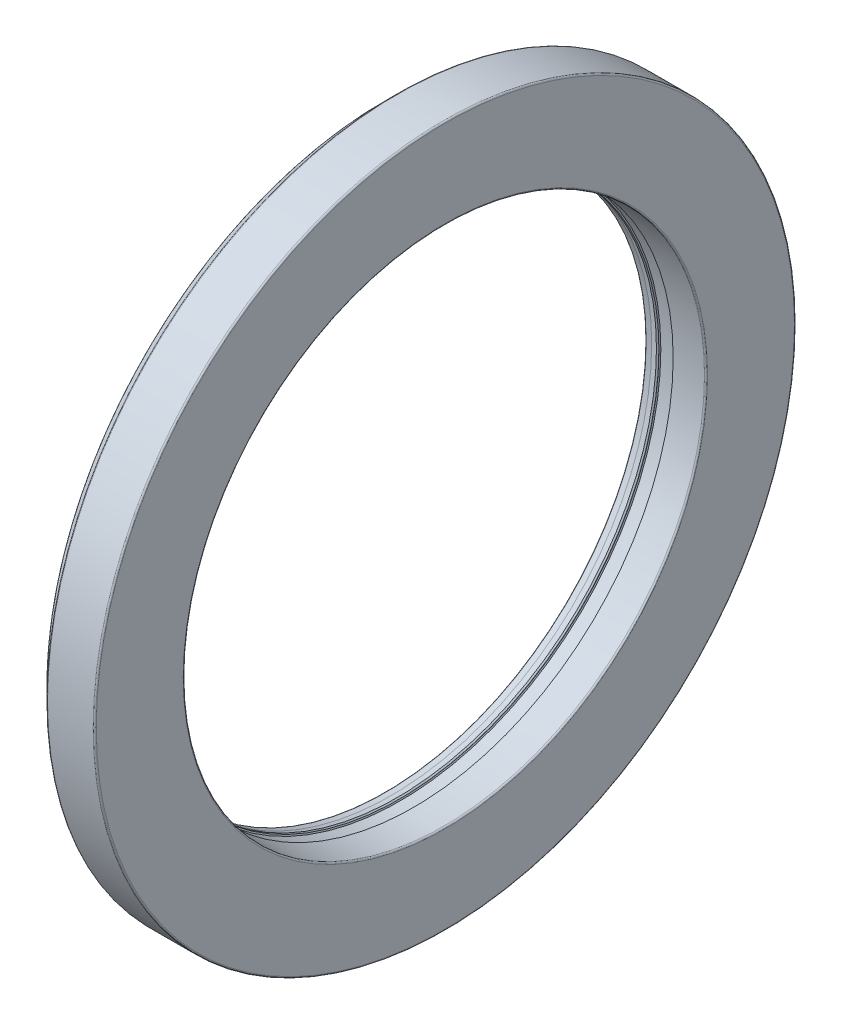
SolidWorks part; units mm, degrees
ref_plane "Piano frontale" through (0, 0, 0) normal (0, 0, 1) x (1, 0, 0)
ref_plane "Piano superiore" through (0, 0, 0) normal (0, 1, 0) x (1, 0, 0)
ref_plane "Piano destro" through (0, 0, 0) normal (1, 0, 0) x (0, 0, -1)
sketch "Schizzo1" plane through (0, 0, 0) normal (0, 0, 1) x (1, 0, 0)
  line L1 (-7.9854, 11.1004) -> (-7.6004, 11.4854)
  line L2 (-7.5651, 11.5) -> (-6.0683, 11.5)
  line L3 (-6.0183, 11.45) -> (-6.0183, 8.598)
  line L5 (-7.98, 8.55) -> (-7.8, 8.55)
  line L6 (-7.8, 8.55) -> (-7.604, 8.51)
  line L8 (-7.604, 8.51) -> (-7.5625, 8.55)
  line L9 (-7.5625, 8.55) -> (-7.542, 8.55)
  line L10 (-7.542, 8.55) -> (-7.5209, 8.5084)
  line L11 (-7.5209, 8.5084) -> (-7.4998, 8.55)
  line L12 (-7.4998, 8.55) -> (-7.0755, 8.55)
  line L13 (-7.0755, 8.55) -> (-7.0543, 8.5084)
  line L14 (-7.0543, 8.5084) -> (-6.0662, 8.5481)
  line L20 (-8, 9.3228) -> (-8, 11.0651)
  line L21 (0, 0) -> (-13.3968, 0) construction
  line L22 (-8, 8.57) -> (-8, 8.8544)
  line L23 (-7.956, 8.904) -> (-6.7894, 9.0444)
  line L24 (-6.7454, 9.0941) -> (-6.7454, 9.3168)
  line L25 (-6.7954, 9.3668) -> (-7.0829, 9.3668)
  line L26 (-7.1329, 9.3168) -> (-7.1329, 9.2928)
  line L27 (-7.1529, 9.2728) -> (-7.95, 9.2728)
  arc A0 (-6.0662, 8.5481) -> (-6.0183, 8.598) centre (-6.0683, 8.598) ccw
  arc A1 (-6.0183, 11.45) -> (-6.0683, 11.5) centre (-6.0683, 11.45) ccw
  arc A2 (-7.5651, 11.5) -> (-7.6004, 11.4854) centre (-7.5651, 11.45) ccw
  arc A3 (-7.9854, 11.1004) -> (-8, 11.0651) centre (-7.95, 11.0651) ccw
  arc A10 (-8, 8.8544) -> (-7.956, 8.904) centre (-7.95, 8.8544) cw
  arc A11 (-7.95, 9.2728) -> (-8, 9.3228) centre (-7.95, 9.3228) cw
  arc A12 (-7.1329, 9.3168) -> (-7.0829, 9.3668) centre (-7.0829, 9.3168) cw
  arc A13 (-6.7894, 9.0444) -> (-6.7454, 9.0941) centre (-6.7954, 9.0941) ccw
  arc A14 (-6.7454, 9.3168) -> (-6.7954, 9.3668) centre (-6.7954, 9.3168) ccw
  arc A15 (-7.1529, 9.2728) -> (-7.1329, 9.2928) centre (-7.1529, 9.2928) ccw
  arc A16 (-8, 8.57) -> (-7.98, 8.55) centre (-7.98, 8.57) ccw
  point P43 (-8, 8.55)
  dimension "D4" = 0.04
  dimension "D5" = 0.05
  dimension "D2" = 0.2
  dimension "D3" = 0.2
  dimension "D6" = 0.05
  dimension "D7" = 0.02
  dimension "D8" = 0.02
  dimension "D1" = 8.55
revolve "Rivoluzione1" add sketch "Schizzo1" angle 360 about L21
